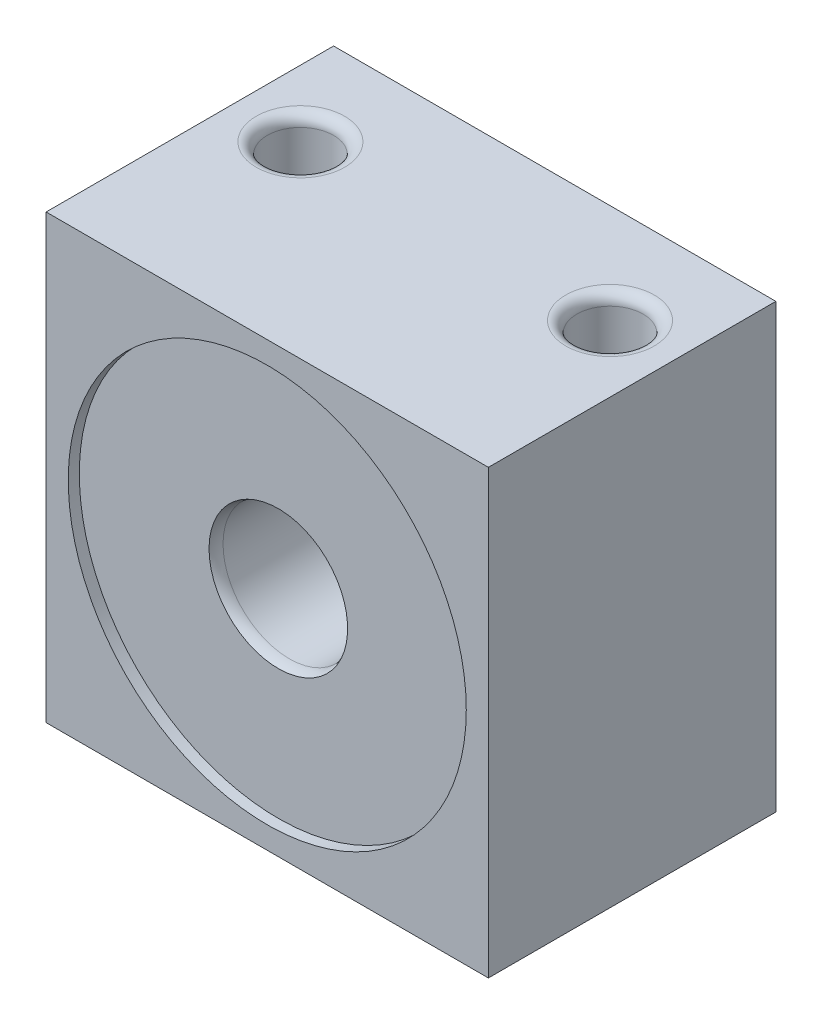
SolidWorks part; units mm, degrees
ref_plane "Plan de face" through (0, 0, 0) normal (0, 0, 1) x (1, 0, 0)
ref_plane "Plan de dessus" through (0, 0, 0) normal (0, 1, 0) x (1, 0, 0)
ref_plane "Plan de droite" through (0, 0, 0) normal (1, 0, 0) x (0, 0, -1)
sketch "Esquisse1" plane through (0, 0, 0) normal (0, 1, 0) x (1, 0, 0)
  line L1 (-10, 6.5) -> (10, 6.5)
  line L2 (-10, 6.5) -> (-10, -6.5)
  line L3 (-10, -6.5) -> (10, -6.5)
  line L4 (10, 6.5) -> (10, -6.5)
  dimension "D1" = 20
  dimension "D2" = 10
  dimension "D3" = 13
  dimension "D4" = 6.5
extrude "Boss.-Extru.1" add sketch "Esquisse1" along normal blind 20
sketch "Esquisse2" plane through (0, 0, 6.5) normal (0, 0, 1) x (1, 0, 0)
  line L0 (-10, 20) -> (10, 20) construction
  line L1 (10, 20) -> (10, 0) construction
  circle A0 centre (0, 10) radius 3
  dimension "D1" = 10
  dimension "D3" = 6
  dimension "D2" = 10
extrude "Enlèv. mat.-Extru.1" cut sketch "Esquisse2" against normal blind 20
sketch "Esquisse3" plane through (0, 20, 0) normal (0, 1, 0) x (1, 0, 0)
  line L0 (-10, -6.5) -> (10, -6.5) construction
  line L1 (-10, 6.5) -> (-10, -6.5) construction
  line L2 (0, 7.1252) -> (0, -6.7854) construction
  circle A0 centre (-7, 2) radius 1.5
  circle A1 centre (7, 2) radius 1.5
  dimension "D1" = 3
  dimension "D2" = 8.5
  dimension "D3" = 3
extrude "Enlèv. mat.-Extru.2" cut sketch "Esquisse3" against normal blind 20
fillet "Congé1" radius 1 1 edges at (3, 10, 6.5)
fillet "Congé2" radius 0.5 1 edges at (-7, 20, -0.5)
fillet "Congé3" radius 0.5 1 edges at (7, 20, -3.5)
fillet "Congé4" radius 0.5 1 edges at (-7, 0, -0.5)
fillet "Congé5" radius 0.5 1 edges at (7, 0, -3.5)
fillet "Congé6" radius 1 1 edges at (3, 10, -6.5)
sketch "Esquisse4" plane through (0, 0, 6.5) normal (0, 0, 1) x (1, 0, 0)
  circle A0 centre (0, 10) radius 3
  circle A1 centre (0, 10) radius 9
  dimension "D1" = 18
  dimension "D2" = 6
extrude "Enlèv. mat.-Extru.3" cut sketch "Esquisse4" against normal blind 0.5
mirror "Symétrie1" about plane through (0, 0, 0) normal (0, 0, 1) of "Enlèv. mat.-Extru.3"
